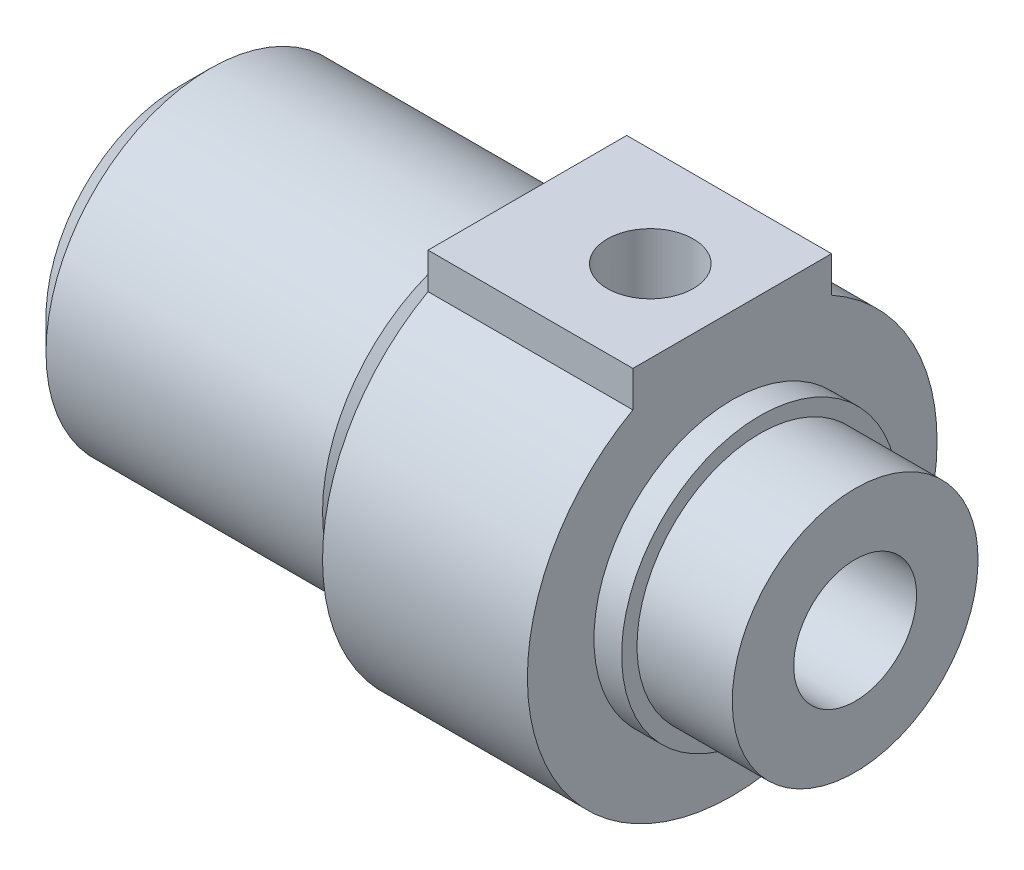
SolidWorks part; units mm, degrees
material "6061-T6 (SS)"
ref_plane "Front Plane" through (0, 0, 0) normal (0, 0, 1) x (1, 0, 0)
ref_plane "Top Plane" through (0, 0, 0) normal (0, 1, 0) x (1, 0, 0)
ref_plane "Right Plane" through (0, 0, 0) normal (1, 0, 0) x (0, 0, -1)
sketch "Sketch1" plane through (0, 0, 0) normal (1, 0, 0) x (0, 0, -1)
  line L0 (0, 0) -> (0, 17.9915) construction
  line L1 (-4.85, 8.7451) -> (-4.85, 10.5)
  line L2 (4.85, 8.7451) -> (4.85, 10.5)
  line L6 (-4.85, 10.5) -> (4.85, 10.5)
  arc A0 (-4.85, 8.7451) -> (4.85, 8.7451) centre (0, 0) ccw
  dimension "RM DIAD2" = 20
  dimension "RMD1" = 9.7
  dimension "RM HEOGHT D3" = 20.5
extrude "Boss-Extrude1" add sketch "Sketch1" along normal blind 33
sketch "Sketch2" plane through (0, 0, 0) normal (0, 0, 1) x (1, 0, 0)
  line L0 (27, 14) -> (27, 6.75)
  line L1 (27, 6.75) -> (28.35, 6.75)
  line L2 (28.35, 6.75) -> (28.35, 6)
  line L3 (28.35, 6) -> (33, 6)
  line L4 (33, -10) -> (33, 8.7451) construction
  line L5 (33, 6) -> (33, 14)
  line L6 (33, 0) -> (0, 0) construction
  line L7 (27, 14) -> (33, 14)
  line L8 (45.5, 0) -> (0, 0) construction
  dimension "BARREL STEP D1" = 13.5
  dimension "BARREL DIA D2" = 12
  dimension "BARREL GUIDED3" = 4.65
  dimension "BARREL EXTRA D4" = 6
  dimension "BARREL SUMA D5" = 8
revolve "Cut-Revolve1" cut sketch "Sketch2" angle 360 about L8
sketch "Sketch3" plane through (0, 0, 0) normal (0, 0, 1) x (1, 0, 0)
  line L0 (0, 0) -> (15.0791, 0) construction
  line L1 (0, 8.7451) -> (0, -10) construction
  line L2 (0, 8) -> (15, 8)
  line L3 (15, 8) -> (15.5, 7.5)
  line L4 (0, 8) -> (0, 16)
  line L5 (0, 16) -> (17, 16)
  line L6 (15.5, 7.5) -> (17, 7.5)
  line L7 (17, 7.5) -> (17, 16)
  line L10 (27, 0) -> (0, 0) construction
  dimension "THREAD SUMA D1" = 8
  dimension "THREAD DIA D2" = 16
  dimension "THREAD LENGTH D3" = 17
  dimension "THREAD ANGLED4" = 45
  dimension "THREAD GROOVE WIDTHD5" = 1.5
  dimension "THREAD GROOVE DIAD6" = 15
revolve "Cut-Revolve2" cut sketch "Sketch3" angle 360 about L0
cosmetic thread "Cosmetic Thread1" parameters "THREAD SIZE D2"=10.072
chamfer "Chamfer1" distance 1.5 angle 45 1 edges at (0, 0, 8)
hole_wizard "G1/8 Tapped Hole1" positions "Sketch5" profile "Sketch4" tap size "G1/8" standard "BSI"
sketch "Sketch5" plane through (0, 10.5, 0) normal (0, 1, 0) x (-1, 0, 0)
  line L0 (-28.35, 6.75) -> (-28.35, -6.75) construction
  line L6 (-15, 0) -> (-1.5, 0) construction
  point P0 (-23, 0)
  dimension "HOLE LOCATION D1" = 5.35
sketch "Sketch4" plane through (23, 10.5, 0) normal (1, 0, 0) x (0, 0, 1)
  line L0 (0, 0) -> (0, 12.2618)
  line L1 (0, 12.2618) -> (2.1, 11)
  line L2 (2.1, 11) -> (2.1, 0)
  line L5 (2.1, 0) -> (0, 0)
  line L10 (0, 12.2618) -> (-2.1, 11) construction
  line L11 (0, -6.35) -> (0, 107.95) construction
  dimension "Tap Drill Dia." = 4.2
  dimension "Tap Drill Depth" = 11
  dimension "Drill Angle" = 118
cosmetic thread "Hole Thread1" parameters "D1"=12, "D2"=5
sketch "Sketch6" plane through (33, 0, 0) normal (1, 0, 0) x (0, 0, -1)
  circle A0 centre (0, 0) radius 3
  dimension "PISTON ROD SIZE D1" = 6
extrude "Cut-Extrude1" cut sketch "Sketch6" against normal through all
sketch "Sketch7" plane through (27, 0, 0) normal (1, 0, 0) x (0, 0, -1)
  line L0 (0, 0) -> (0, 10.5) construction
  line L1 (-4.3116, 7.9) -> (4.3116, 7.9)
  line L2 (-7.9, 4.3116) -> (-7.9, -4.3116)
  line L3 (-4.3116, -7.9) -> (4.3116, -7.9)
  line L4 (7.9, 4.3116) -> (7.9, -4.3116)
  line L5 (-6.364, 6.364) -> (6.364, -6.364) construction
  line L6 (-6.364, -6.364) -> (6.364, 6.364) construction
  line L7 (-4.85, 10.5) -> (4.85, 10.5) construction
  line L8 (0, 0) -> (10, 0) construction
  line L10 (-12.5, 12.5) -> (12.5, 12.5)
  line L11 (-12.5, 12.5) -> (-12.5, -12.5)
  line L12 (-12.5, -12.5) -> (12.5, -12.5)
  line L13 (12.5, 12.5) -> (12.5, -12.5)
  line L14 (-12.5, 12.5) -> (12.5, -12.5) construction
  line L15 (-12.5, -12.5) -> (12.5, 12.5) construction
  arc A0 (-4.3116, 7.9) -> (-7.9, 4.3116) centre (0, 0) ccw
  arc A1 (-7.9, -4.3116) -> (-4.3116, -7.9) centre (0, 0) ccw
  arc A2 (7.9, 4.3116) -> (4.3116, 7.9) centre (0, 0) ccw
  arc A3 (4.3116, -7.9) -> (7.9, -4.3116) centre (0, 0) ccw
  arc A4 (-4.85, 8.7451) -> (4.85, 8.7451) centre (0, 0) ccw construction
  point P0 (0, 0)
  dimension "D1" = 18
  dimension "D2" = 15.8
  dimension "D3" = 15.8
  dimension "D4" = 25
  dimension "D5" = 25
extrude "Cut-Extrude2" [suppressed] cut sketch "Sketch7" against normal through all
